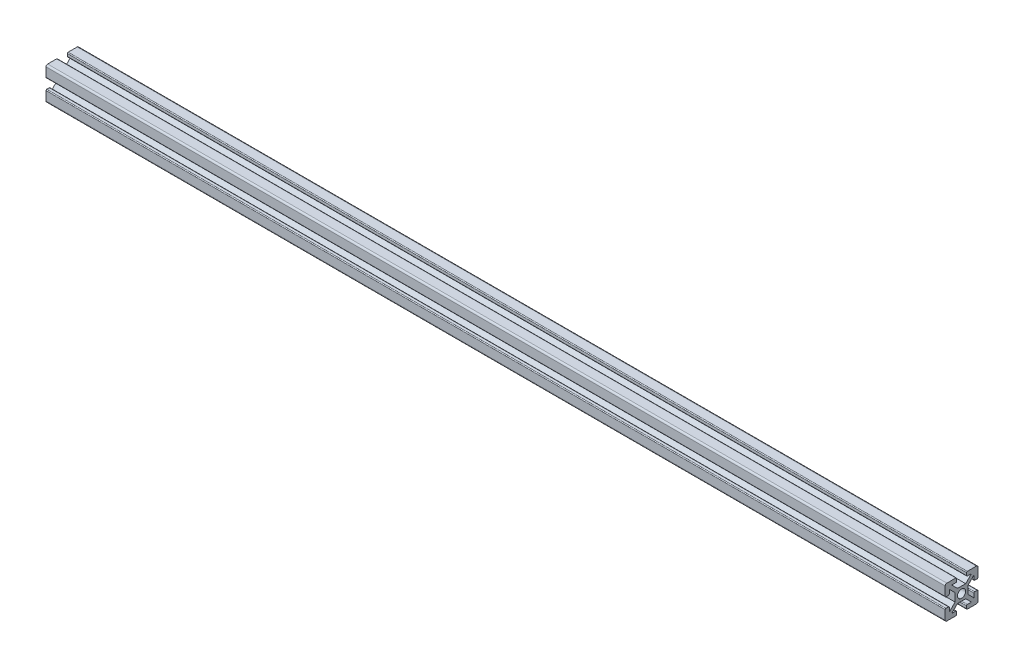
SolidWorks part; units mm, degrees
ref_plane "Front Plane" through (0, 0, 0) normal (0, 0, 1) x (1, 0, 0)
ref_plane "Top Plane" through (0, 0, 0) normal (0, 1, 0) x (1, 0, 0)
ref_plane "Right Plane" through (0, 0, 0) normal (1, 0, 0) x (0, 0, -1)
sketch "Sketch1" plane through (0, 0, 0) normal (0, 0, 1) x (1, 0, 0)
  line L0 (-263.7963, 0) -> (286.2037, 0)
  dimension "D1" = 550
other "Aluminium prof ALUMINIUM PROF(1)"
ref_plane "Plane1" through (-263.7963, 0, 0) normal (1, 0, 0) x (0, 1, 0)
sketch "Sketch11" plane through (-263.7963, 0, 0) normal (1, 0, 0) x (0, 1, 0)
  line L0 (0, 0) -> (0, 19.0058) construction
  line L9 (0, 0) -> (23.0409, 0) construction
  line L10 (23.0409, 0) -> (23.0409, -0.0585) construction
  line L11 (23.0409, -0.0585) -> (23.0409, 0) construction
  line L13 (-2.5, 4) -> (2.5, 4)
  line L14 (2.5, 4) -> (6.0355, 7.5355)
  line L15 (6.0355, 7.5355) -> (3.5355, 7.5355)
  line L16 (3.0355, 8.0355) -> (3.0355, 9.5355)
  line L17 (3.5355, 10.0355) -> (9.0355, 10.0355)
  line L18 (10.0355, 9.0355) -> (10.0355, 3.5355)
  line L19 (9.5355, 3.0355) -> (8.0355, 3.0355)
  line L20 (7.5355, 3.5355) -> (7.5355, 6.0355)
  line L21 (7.5355, 6.0355) -> (4, 2.5)
  line L22 (4, 2.5) -> (4, -2.5)
  line L23 (-10.0355, 9.0355) -> (-10.0355, 3.5355)
  line L24 (-4, 2.5) -> (-4, -2.5)
  line L25 (-7.5355, 6.0355) -> (-4, 2.5)
  line L26 (-7.5355, 3.5355) -> (-7.5355, 6.0355)
  line L27 (-9.5355, 3.0355) -> (-8.0355, 3.0355)
  line L28 (-3.5355, 10.0355) -> (-9.0355, 10.0355)
  line L29 (-3.0355, 8.0355) -> (-3.0355, 9.5355)
  line L30 (-6.0355, 7.5355) -> (-3.5355, 7.5355)
  line L31 (-2.5, 4) -> (-6.0355, 7.5355)
  line L32 (3.5355, -10.0355) -> (9.0355, -10.0355)
  line L33 (-2.5, -4) -> (-6.0355, -7.5355)
  line L34 (-6.0355, -7.5355) -> (-3.5355, -7.5355)
  line L35 (-3.0355, -8.0355) -> (-3.0355, -9.5355)
  line L36 (-3.5355, -10.0355) -> (-9.0355, -10.0355)
  line L37 (-9.5355, -3.0355) -> (-8.0355, -3.0355)
  line L38 (-7.5355, -3.5355) -> (-7.5355, -6.0355)
  line L39 (-7.5355, -6.0355) -> (-4, -2.5)
  line L40 (-10.0355, -9.0355) -> (-10.0355, -3.5355)
  line L41 (7.5355, -6.0355) -> (4, -2.5)
  line L42 (7.5355, -3.5355) -> (7.5355, -6.0355)
  line L43 (9.5355, -3.0355) -> (8.0355, -3.0355)
  line L44 (10.0355, -9.0355) -> (10.0355, -3.5355)
  line L45 (3.0355, -8.0355) -> (3.0355, -9.5355)
  line L46 (6.0355, -7.5355) -> (3.5355, -7.5355)
  line L47 (2.5, -4) -> (6.0355, -7.5355)
  line L48 (-2.5, -4) -> (2.5, -4)
  circle A0 centre (0, 0) radius 2.5
  arc A1 (-10.0355, 9.0355) -> (-9.0355, 10.0355) centre (-9.0355, 9.0355) cw
  arc A2 (-9.0355, -10.0355) -> (-10.0355, -9.0355) centre (-9.0355, -9.0355) cw
  arc A3 (9.0355, -10.0355) -> (10.0355, -9.0355) centre (9.0355, -9.0355) ccw
  arc A4 (9.0355, 10.0355) -> (10.0355, 9.0355) centre (9.0355, 9.0355) cw
  arc A5 (-9.5355, -3.0355) -> (-10.0355, -3.5355) centre (-9.5355, -3.5355) ccw
  arc A6 (-8.0355, -3.0355) -> (-7.5355, -3.5355) centre (-8.0355, -3.5355) cw
  arc A7 (-3.5355, -7.5355) -> (-3.0355, -8.0355) centre (-3.5355, -8.0355) cw
  arc A8 (-3.0355, -9.5355) -> (-3.5355, -10.0355) centre (-3.5355, -9.5355) cw
  arc A9 (3.5355, -10.0355) -> (3.0355, -9.5355) centre (3.5355, -9.5355) cw
  arc A10 (3.0355, -8.0355) -> (3.5355, -7.5355) centre (3.5355, -8.0355) cw
  arc A11 (9.5355, -3.0355) -> (10.0355, -3.5355) centre (9.5355, -3.5355) cw
  arc A12 (7.5355, -3.5355) -> (8.0355, -3.0355) centre (8.0355, -3.5355) cw
  arc A13 (10.0355, 3.5355) -> (9.5355, 3.0355) centre (9.5355, 3.5355) cw
  arc A14 (8.0355, 3.0355) -> (7.5355, 3.5355) centre (8.0355, 3.5355) cw
  arc A15 (3.5355, 7.5355) -> (3.0355, 8.0355) centre (3.5355, 8.0355) cw
  arc A16 (3.0355, 9.5355) -> (3.5355, 10.0355) centre (3.5355, 9.5355) cw
  arc A17 (-3.5355, 10.0355) -> (-3.0355, 9.5355) centre (-3.5355, 9.5355) cw
  arc A18 (-3.0355, 8.0355) -> (-3.5355, 7.5355) centre (-3.5355, 8.0355) cw
  arc A19 (-7.5355, 3.5355) -> (-8.0355, 3.0355) centre (-8.0355, 3.5355) cw
  arc A20 (-10.0355, 3.5355) -> (-9.5355, 3.0355) centre (-9.5355, 3.5355) ccw
  point P26 (0, 4)
  point P29 (-4, 0)
  point P30 (4, 0)
  point P44 (0, -4)
  point P48 (-10.0355, 10.0355)
  point P51 (-10.0355, -10.0355)
  point P54 (10.0355, -10.0355)
  point P57 (10.0355, 10.0355)
  point P60 (-10.0355, -3.0355)
  point P63 (-7.5355, -3.0355)
  point P66 (-3.0355, -7.5355)
  point P69 (-3.0355, -10.0355)
  point P72 (3.0355, -10.0355)
  point P75 (3.0355, -7.5355)
  point P78 (10.0355, -3.0355)
  point P81 (7.5355, -3.0355)
  point P84 (10.0355, 3.0355)
  point P87 (7.5355, 3.0355)
  point P90 (3.0355, 7.5355)
  point P93 (3.0355, 10.0355)
  point P96 (-3.0355, 10.0355)
  point P99 (-3.0355, 7.5355)
  point P102 (-7.5355, 3.0355)
  point P105 (-10.0355, 3.0355)
  point P106 (0, 0)
  dimension "D5" = 4
  dimension "D12" = 1
  dimension "D13" = 0.5
  dimension "D1" = 135
  dimension "D2" = 2.5
  dimension "D3" = 4
  dimension "D4" = 2.5
  dimension "D6" = 7
  dimension "D7" = 7
  dimension "D8" = 3
  dimension "D9" = 3
  dimension "D10" = 5
  dimension "D11" = 23.0409
sketch "Sketch12" plane through (0, 4, 0) normal (0, 1, 0) x (1, 0, 0)
  line L0 (11.2037, 2.5) -> (11.2037, -2.5) construction
  line L1 (286.2037, 2.5) -> (-263.7963, 2.5) construction
  line L2 (286.2037, -2.5) -> (-263.7963, -2.5) construction
  line L3 (11.2037, 0) -> (28.8289, 0) construction
  circle A0 centre (-248.7963, 0) radius 2.5
  circle A1 centre (271.2037, 0) radius 2.5
  point P13 (0, 0)
  dimension "D1" = 5
  dimension "D2" = 520
extrude "Cut-Extrude1" cut sketch "Sketch12" against normal through all
equation "\"u5\"=4.99781"
